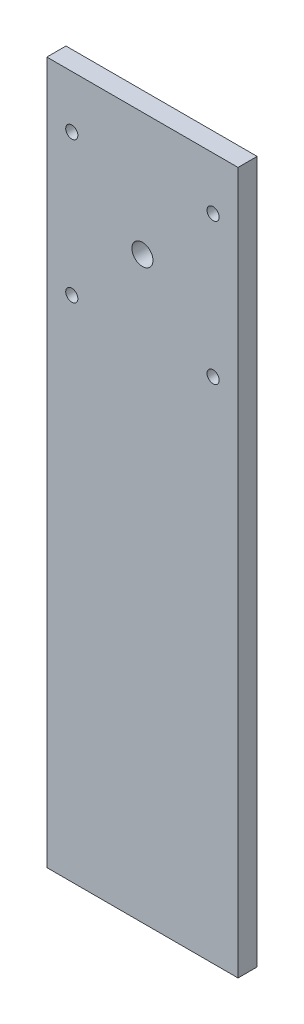
SolidWorks part; units mm, degrees
ref_plane "Front Plane" through (0, 0, 0) normal (0, 0, 1) x (1, 0, 0)
ref_plane "Top Plane" through (0, 0, 0) normal (0, 1, 0) x (1, 0, 0)
ref_plane "Right Plane" through (0, 0, 0) normal (1, 0, 0) x (0, 0, -1)
sketch "Sketch1" plane through (0, 0, 0) normal (0, 0, 1) x (1, 0, 0)
  line L1 (0, 0) -> (63.5, 0)
  line L2 (0, 0) -> (0, -233.172)
  line L3 (0, -233.172) -> (63.5, -233.172)
  line L4 (63.5, 0) -> (63.5, -233.172)
  circle A0 centre (31.75, -40.894) radius 3.4925
  point P11 (31.75, 0)
  dimension "D4" = 6.985
  dimension "D5" = 192.278
  dimension "D1" = 63.5
  dimension "D2" = 233.172
extrude "Boss-Extrude1" add sketch "Sketch1" along normal blind 6.35
sketch "Sketch6" plane through (0, 0, 6.35) normal (0, 0, 1) x (1, 0, 0)
  line L0 (8.2804, -17.4244) -> (55.2196, -17.4244) construction
  line L1 (55.2196, -17.4244) -> (55.2196, -64.3636) construction
  line L2 (55.2196, -64.3636) -> (8.2804, -64.3636) construction
  line L3 (8.2804, -64.3636) -> (8.2804, -17.4244) construction
  line L4 (63.5, 0) -> (0, 0) construction
  line L5 (28.2575, -40.894) -> (35.2425, -40.894) construction
  circle A0 centre (31.75, -40.894) radius 3.4925 construction
  point P0 (8.2804, -17.4244)
  point P1 (55.2196, -17.4244)
  point P2 (55.2196, -64.3636)
  point P3 (8.2804, -64.3636)
  point P10 (8.2804, -40.894)
  point P11 (31.75, -17.4244)
  point P13 (31.75, 0)
  dimension "D1" = 46.9392
hole_wizard "#10-32 Tapped Hole1" positions "Sketch8" profile "Sketch7" tap size "#10-32" standard "ANSI Inch" end condition up to next
sketch "Sketch8" plane through (0, 0, 6.35) normal (0, 0, 1) x (1, 0, 0)
  point P0 (8.2804, -17.4244)
  point P3 (55.2196, -17.4244)
  point P6 (55.2196, -64.3636)
  point P9 (8.2804, -64.3636)
cosmetic thread "Hole Thread1" parameters "D2"=4.826
cosmetic thread "Hole Thread2" parameters "D2"=4.826
cosmetic thread "Hole Thread3" parameters "D2"=4.826
cosmetic thread "Hole Thread4" parameters "D2"=4.826
sketch "Sketch7" plane through (8.2804, -17.4244, 6.35) normal (1, 0, 0) x (0, -1, 0)
  line L0 (0, 0) -> (0, 6.35)
  line L1 (0, 6.35) -> (2.0193, 6.35)
  line L2 (2.0193, 6.35) -> (2.0193, 0)
  line L5 (2.0193, 0) -> (0, 0)
  line L11 (0, -6.35) -> (0, 107.95) construction
  dimension "Thru Tap Drill Dia." = 4.0386
  dimension "Thru Tap Drill Depth" = 6.35
